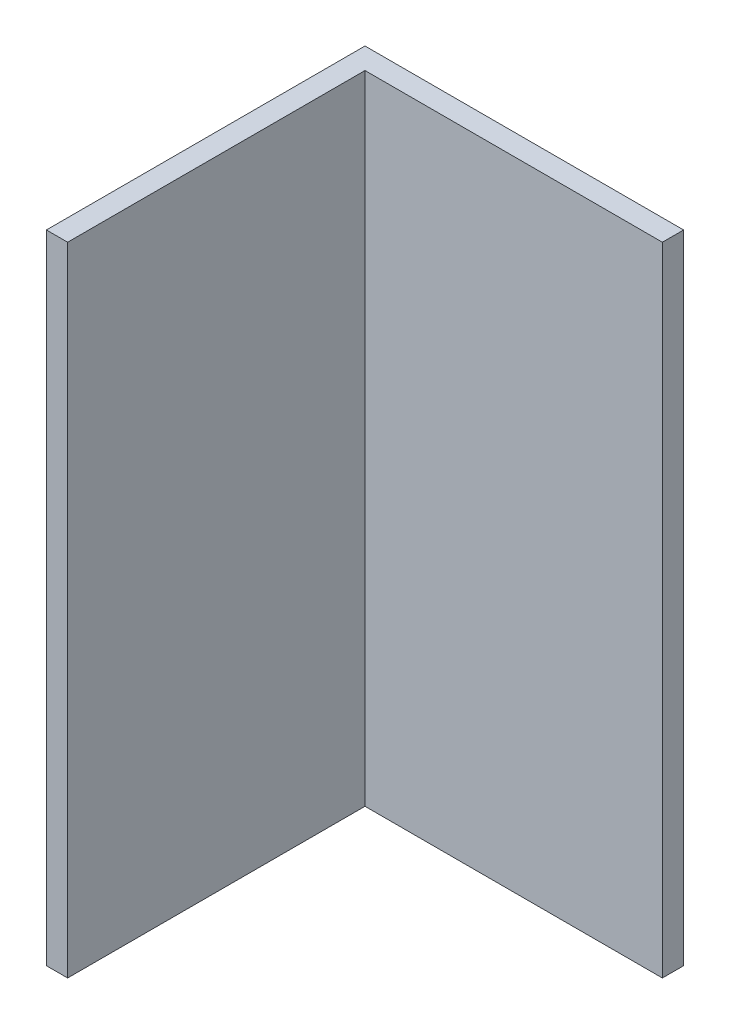
SolidWorks part; units mm, degrees
ref_plane "Front Plane" through (0, 0, 0) normal (0, 0, 1) x (1, 0, 0)
ref_plane "Top Plane" through (0, 0, 0) normal (0, 1, 0) x (1, 0, 0)
ref_plane "Right Plane" through (0, 0, 0) normal (1, 0, 0) x (0, 0, -1)
sketch "Sketch1" plane through (0, 0, 0) normal (0, 1, 0) x (1, 0, 0)
  line L0 (0, 0) -> (0, -30)
  line L1 (0, 0) -> (30, 0)
  line L3 (2, -2) -> (30, -2)
  line L4 (30, 0) -> (30, -2)
  line L7 (0, -30) -> (2, -30)
  line L8 (2, -2) -> (2, -30)
  dimension "D1" = 2
  dimension "D2" = 30
extrude "Boss-Extrude1" add sketch "Sketch1" along normal blind 60
